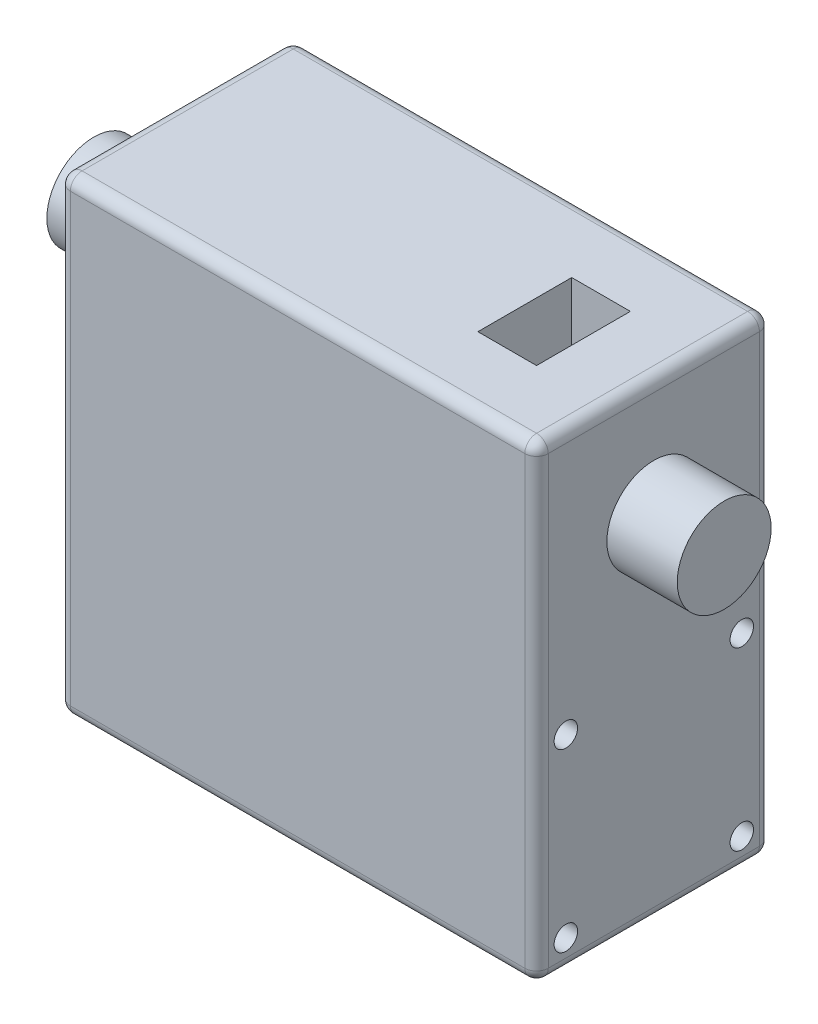
SolidWorks part; units mm, degrees
ref_plane "Front Plane" through (0, 0, 0) normal (0, 0, 1) x (1, 0, 0)
ref_plane "Top Plane" through (0, 0, 0) normal (0, 1, 0) x (1, 0, 0)
ref_plane "Right Plane" through (0, 0, 0) normal (1, 0, 0) x (0, 0, -1)
sketch "Sketch1" plane through (0, 0, 0) normal (0, 0, 1) x (1, 0, 0)
  line L1 (0, 0) -> (40.7459, 0)
  line L2 (0, 0) -> (0, 40)
  line L3 (0, 40) -> (40.7459, 40)
  line L4 (40.7459, 0) -> (40.7459, 40)
  dimension "D1" = 40.7459
  dimension "D2" = 40
extrude "Boss-Extrude1" add sketch "Sketch1" along normal blind 20
fillet "Fillet1" radius 1 12 edges at (0, 20, 0) (0, 20, 20) (40.7459, 20, 0) (40.7459, 20, 20) (40.7459, 0, 10) (40.7459, 40, 10) (0, 0, 10) (0, 40, 10) (20.373, 0, 0) (20.373, 0, 20) (20.373, 40, 0) (20.373, 40, 20)
sketch "Sketch2" plane through (40.7459, 0, 0) normal (1, 0, 0) x (0, 0, -1)
  line L0 (-19, 40) -> (-1, 40) construction
  line L1 (-19, 40) -> (-1, 40) construction
  circle A0 centre (-10, 30) radius 4
  point P5 (-10, 40)
  dimension "D2" = 8
  dimension "D1" = 10
extrude "Boss-Extrude2" add sketch "Sketch2" along normal blind 6
sketch "Sketch3" plane through (0, 40, 0) normal (0, 1, 0) x (1, 0, 0)
  line L0 (40.7459, -1) -> (40.7459, -19) construction
  line L1 (40.7459, -1) -> (40.7459, -19) construction
  line L2 (29.7459, -1) -> (29.7459, -19) construction
  line L4 (29.7459, -6) -> (34.7459, -6)
  line L5 (29.7459, -6) -> (29.7459, -14)
  line L6 (29.7459, -14) -> (34.7459, -14)
  line L7 (34.7459, -6) -> (34.7459, -14)
  point P8 (29.7459, -10)
  point P10 (40.7459, -10)
  dimension "D2" = 11
  dimension "D3" = 8
  dimension "D4" = 5
  dimension "D1" = 2
extrude "Cut-Extrude1" cut sketch "Sketch3" against normal blind 5
sketch "Sketch4" plane through (0, 0, 0) normal (-1, 0, 0) x (0, 0, 1)
  line L0 (1, 40) -> (19, 40) construction
  line L1 (1, 40) -> (19, 40) construction
  circle A0 centre (10, 30) radius 4
  point P4 (10, 40)
  dimension "D1" = 8
  dimension "D2" = 10
extrude "Boss-Extrude3" add sketch "Sketch4" along normal blind 7
sketch "Sketch5" plane through (40.7459, 0, 0) normal (1, 0, 0) x (0, 0, -1)
  line L1 (-1, 0) -> (-19, 0) construction
  line L2 (-1, 0) -> (-19, 0) construction
  line L3 (-19, 10) -> (-1, 10) construction
  line L4 (-19, 39) -> (-19, 1) construction
  line L5 (-1, 1) -> (-1, 39) construction
  line L7 (-17.5, 2.5) -> (-2.5, 2.5) construction
  line L8 (-17.5, 2.5) -> (-17.5, 17.5) construction
  line L9 (-17.5, 17.5) -> (-2.5, 17.5) construction
  line L10 (-2.5, 2.5) -> (-2.5, 17.5) construction
  circle A5 centre (-17.5, 17.5) radius 1
  circle A6 centre (-2.5, 17.5) radius 1
  circle A7 centre (-2.5, 2.5) radius 1
  circle A8 centre (-17.5, 2.5) radius 1
  point P8 (-10, 10)
  point P9 (-10, 0)
  point P14 (-10, 2.5)
  point P15 (-17.5, 10)
  dimension "D2" = 15
  dimension "D3" = 2
  dimension "D1" = 10
extrude "Cut-Extrude2" cut sketch "Sketch5" against normal blind 5
sketch "Sketch6" plane through (0, 0, 0) normal (-1, 0, 0) x (0, 0, 1)
  line L0 (19, 0) -> (1, 0) construction
  line L1 (19, 0) -> (1, 0) construction
  circle A0 centre (10, 10) radius 7 construction
  circle A2 centre (17, 10) radius 1
  circle A3 centre (10, 3) radius 1
  circle A4 centre (3, 10) radius 1
  point P4 (10, 0)
  dimension "D2" = 14
  dimension "D3" = 2
  dimension "D1" = 10
extrude "Cut-Extrude3" cut sketch "Sketch6" against normal blind 5
